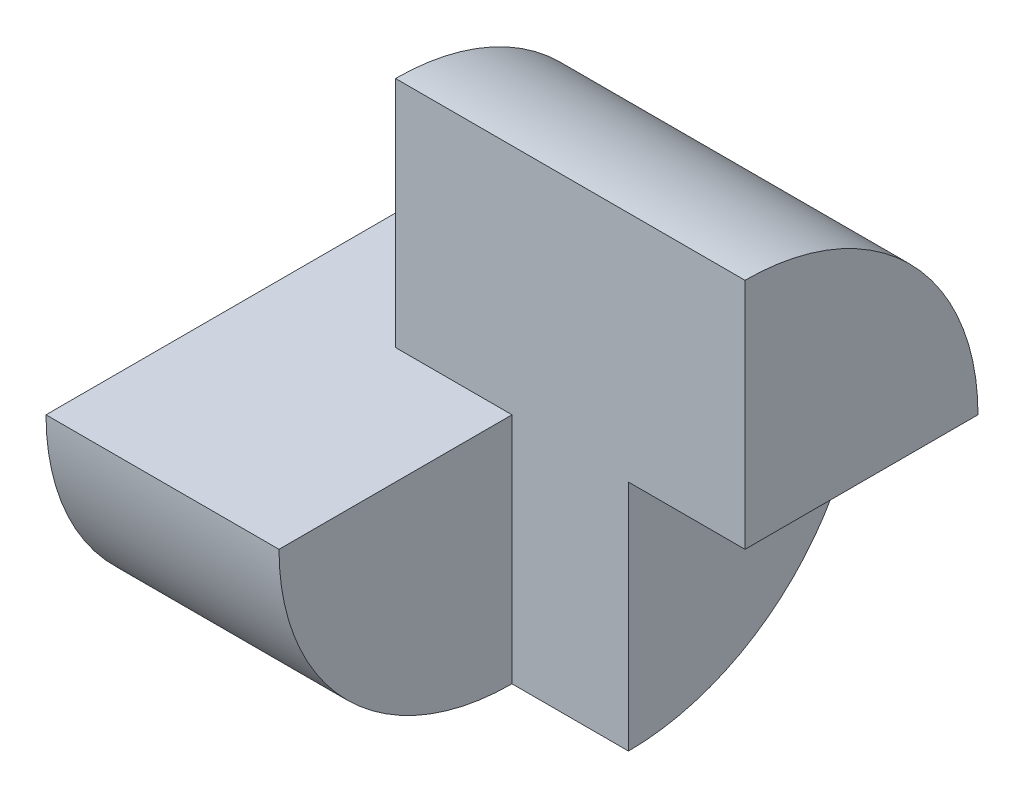
SolidWorks part; units mm, degrees
ref_plane "Front Plane" through (0, 0, 0) normal (0, 0, 1) x (1, 0, 0)
ref_plane "Top Plane" through (0, 0, 0) normal (0, 1, 0) x (1, 0, 0)
ref_plane "Right Plane" through (0, 0, 0) normal (1, 0, 0) x (0, 0, -1)
sketch "Sketch1" plane through (0, 0, 0) normal (0, 0, 1) x (1, 0, 0)
  line L1 (0, 0) -> (40, 0)
  line L2 (0, 0) -> (0, 40)
  line L3 (0, 40) -> (40, 40)
  line L4 (40, 0) -> (40, 40)
  dimension "D1" = 40
  dimension "D2" = 40
extrude "Boss-Extrude1" add sketch "Sketch1" along normal blind 40
sketch "Sketch2" plane through (0, 0, 40) normal (0, 0, 1) x (1, 0, 0)
  line L1 (0, 40) -> (10, 40)
  line L2 (0, 40) -> (0, 20)
  line L3 (0, 20) -> (10, 20)
  line L4 (10, 40) -> (10, 20)
  line L5 (40, 0) -> (30, 0)
  line L6 (40, 0) -> (40, 20)
  line L7 (40, 20) -> (30, 20)
  line L8 (30, 0) -> (30, 20)
  dimension "D1" = 10
  dimension "D2" = 10
  dimension "D3" = 20
  dimension "D4" = 20
extrude "Cut-Extrude1" cut sketch "Sketch2" against normal blind 40
sketch "Sketch3" plane through (10, 0, 0) normal (-1, 0, 0) x (0, 0, 1)
  line L0 (0, 20) -> (40, 20) construction
  line L1 (40, 40) -> (20, 40)
  line L2 (40, 40) -> (40, 20)
  line L3 (40, 20) -> (20, 20)
  line L4 (20, 40) -> (20, 20)
  dimension "D1" = 20
extrude "Cut-Extrude2" cut sketch "Sketch3" against normal blind 40
sketch "Sketch4" plane through (10, 0, 0) normal (-1, 0, 0) x (0, 0, 1)
  line L0 (20, 40) -> (20, 20) construction
  line L1 (20, 40) -> (0, 40)
  line L2 (0, 40) -> (0, 20)
  arc A0 (0, 20) -> (20, 40) centre (20, 20) cw
extrude "Cut-Extrude3" cut sketch "Sketch4" against normal blind 40
sketch "Sketch5" plane through (30, 0, 0) normal (1, 0, 0) x (0, 0, -1)
  line L0 (0, 0) -> (-40, 0) construction
  line L1 (-40, 20) -> (-20, 20)
  line L2 (-40, 20) -> (-40, 0)
  line L3 (-40, 0) -> (-20, 0)
  line L4 (-20, 20) -> (-20, 0)
  dimension "D1" = 20
extrude "Cut-Extrude4" cut sketch "Sketch5" against normal blind 10
sketch "Sketch6" plane through (0, 0, 0) normal (-1, 0, 0) x (0, 0, 1)
  line L0 (0, 20) -> (40, 20) construction
  line L1 (0, 20) -> (0, 0)
  line L2 (0, 0) -> (40, 0)
  line L3 (40, 0) -> (40, 20)
  arc A0 (40, 20) -> (0, 20) centre (20, 20) cw
  line M1 (40, 0) -> (40, 20)
  line M3 (0, 20) -> (0, 0)
  line M4 (0, 0) -> (40, 0)
extrude "Cut-Extrude6" cut sketch "Sketch6" against normal blind 43 contours A0 M4 M3 | A0 L2 M1
